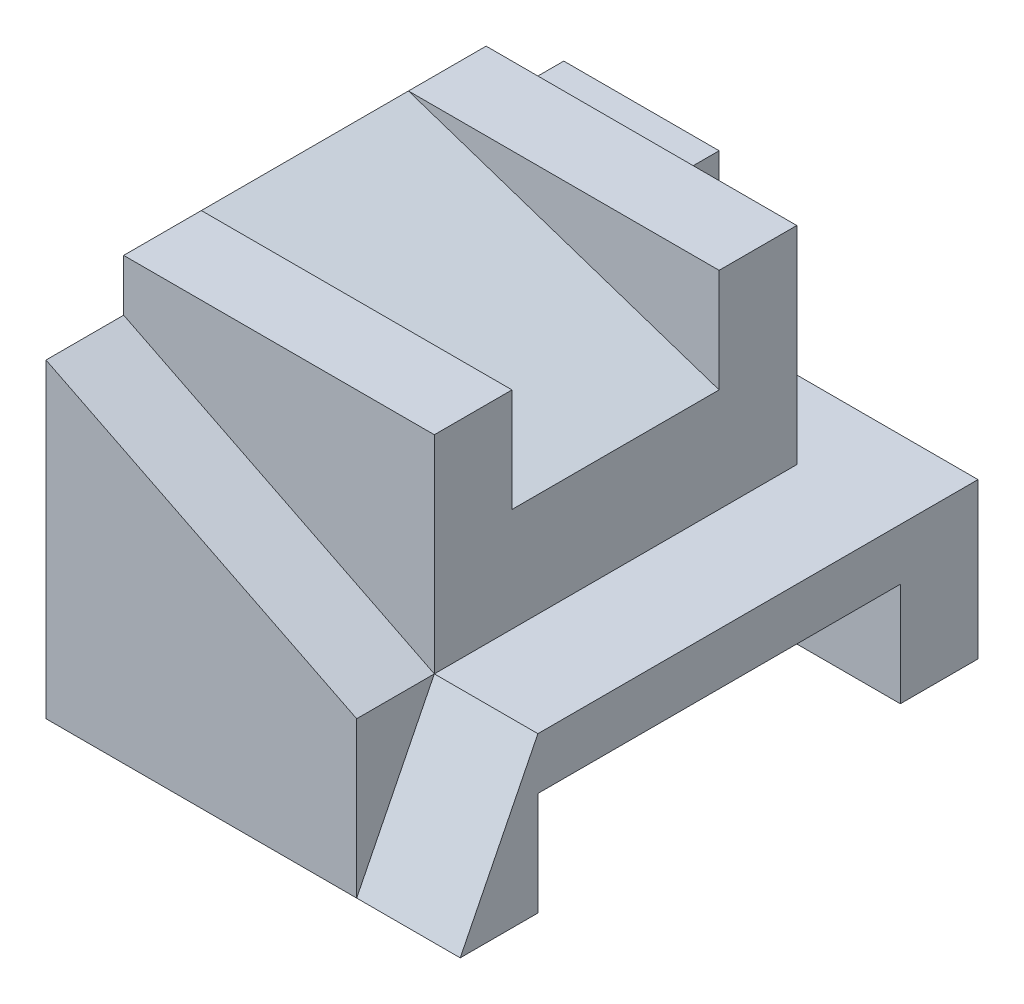
SolidWorks part; units mm, degrees
material "Roble"
ref_plane "Alzado" through (0, 0, 0) normal (0, 0, 1) x (1, 0, 0)
ref_plane "Planta" through (0, 0, 0) normal (0, 1, 0) x (1, 0, 0)
ref_plane "Vista lateral" through (0, 0, 0) normal (1, 0, 0) x (0, 0, -1)
sketch "Croquis1" plane through (0, 0, 0) normal (0, 1, 0) x (1, 0, 0)
  line L1 (-4, 5) -> (4, 5)
  line L2 (-4, 5) -> (-4, -5)
  line L3 (-4, -5) -> (4, -5)
  line L4 (4, 5) -> (4, -5)
  line L5 (-4, 5) -> (4, -5) construction
  line L6 (-4, -5) -> (4, 5) construction
  point P0 (0, 0)
  dimension "D1" = 10
  dimension "D2" = 8
extrude "Saliente-Extruir1" add sketch "Croquis1" along normal blind 3
sketch "Croquis2" plane through (4, 0, 0) normal (1, 0, 0) x (0, 0, -1)
  line L0 (-5, 0) -> (5, 0) construction
  line L1 (-3.5, 0) -> (3.5, 0)
  line L2 (-3.5, 0) -> (-3.5, 2)
  line L3 (-3.5, 2) -> (3.5, 2)
  line L4 (3.5, 0) -> (3.5, 2)
  dimension "D1" = 1.5
  dimension "D2" = 7
  dimension "D3" = 2
extrude "Cortar-Extruir1" cut sketch "Croquis2" against normal through all
sketch "Croquis5" plane through (0, 3, 0) normal (0, 1, 0) x (1, 0, 0)
  line L0 (-4, 5) -> (-4, -5) construction
  line L1 (-4, -3.5) -> (2, -3.5)
  line L2 (-4, -3.5) -> (-4, 3.5)
  line L3 (-4, 3.5) -> (2, 3.5)
  line L4 (2, -3.5) -> (2, 3.5)
  dimension "D1" = 6
  dimension "D2" = 7
  dimension "D3" = 1.5
extrude "Saliente-Extruir2" add sketch "Croquis5" along normal blind 4
sketch "Croquis6" plane through (0, 3, 0) normal (0, 1, 0) x (1, 0, 0)
  line L0 (-4, -5) -> (4, -5) construction
  line L1 (-4, -3.5) -> (2, -3.5)
  line L2 (-4, -3.5) -> (-4, -5)
  line L3 (-4, -5) -> (2, -5)
  line L4 (2, -3.5) -> (2, -5)
  dimension "D1" = 6
extrude "Saliente-Extruir3" add sketch "Croquis6" along normal blind 3
sketch "Croquis7" plane through (0, 0, 5) normal (0, 0, 1) x (1, 0, 0)
  line L0 (2, 3) -> (-4, 6)
  line L1 (-4, 6) -> (2, 6)
  line L2 (2, 6) -> (2, 3)
extrude "Cortar-Extruir2" cut sketch "Croquis7" against normal blind 1.5
sketch "Croquis8" plane through (4, 0, 0) normal (1, 0, 0) x (0, 0, -1)
  line L1 (-5, 3) -> (5, 3) construction
  line L2 (-3.5, 3) -> (-5, 3)
  line L3 (-5, 3) -> (-5, 0)
  line L4 (-5, 0) -> (-3.5, 3)
extrude "Cortar-Extruir3" cut sketch "Croquis8" against normal blind 2
sketch "Croquis9" plane through (0, 3, 0) normal (0, 1, 0) x (1, 0, 0)
  line L0 (4, 5) -> (-4, 5) construction
  line L1 (-4, 3.5) -> (-1, 3.5)
  line L2 (-4, 3.5) -> (-4, 5)
  line L3 (-4, 5) -> (-1, 5)
  line L4 (-1, 3.5) -> (-1, 5)
  dimension "D1" = 3
extrude "Saliente-Extruir4" add sketch "Croquis9" along normal blind 3
sketch "Croquis10" plane through (2, 0, 0) normal (1, 0, 0) x (0, 0, -1)
  line L0 (-3.5, 7) -> (3.5, 7) construction
  line L1 (-2, 7) -> (2, 7)
  line L2 (-2, 7) -> (-2, 5)
  line L3 (-2, 5) -> (2, 5)
  line L4 (2, 7) -> (2, 5)
  dimension "D1" = 1.5
  dimension "D2" = 2
  dimension "D3" = 4
extrude "Cortar-Extruir4" cut sketch "Croquis10" against normal through all
sketch "Croquis11" plane through (0, 0, -2) normal (0, 0, 1) x (1, 0, 0)
  line L0 (2, 5) -> (-4, 5)
  line L1 (-4, 5) -> (-4, 7)
  line L2 (-4, 7) -> (2, 5)
extrude "Saliente-Extruir5" add sketch "Croquis11" along normal blind 4
